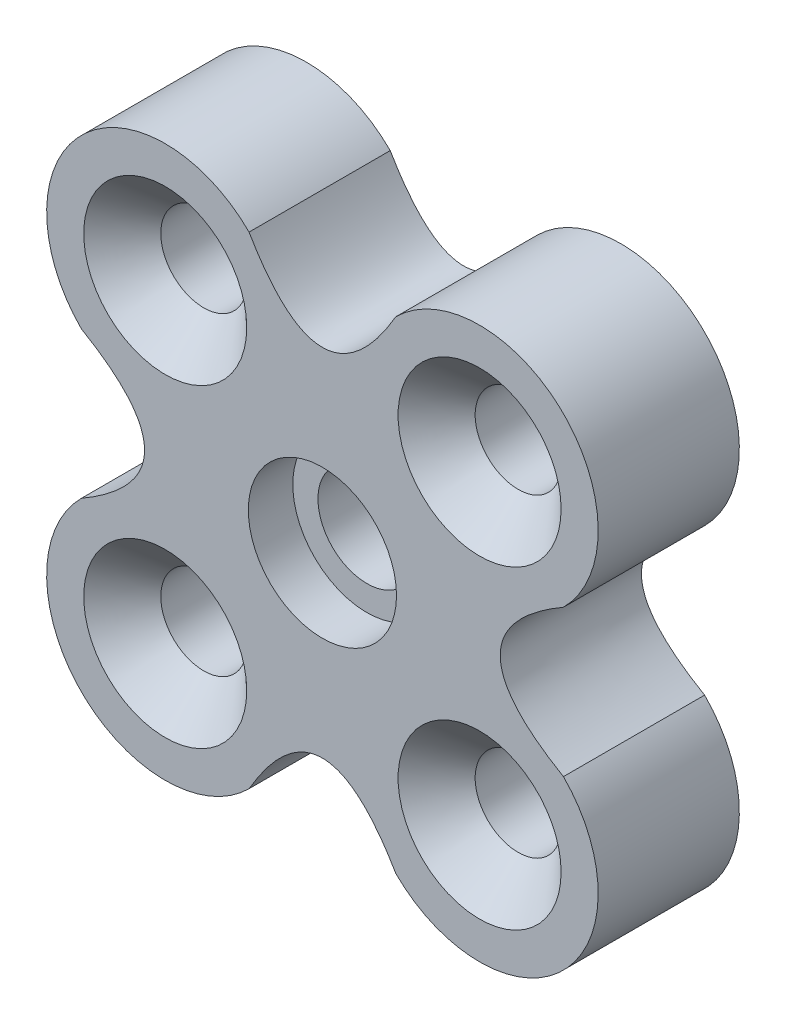
SolidWorks part; units mm, degrees
material "6061-T6 (SS)"
ref_plane "Front Plane" through (0, 0, 0) normal (0, 0, 1) x (1, 0, 0)
ref_plane "Top Plane" through (0, 0, 0) normal (0, 1, 0) x (1, 0, 0)
ref_plane "Right Plane" through (0, 0, 0) normal (1, 0, 0) x (0, 0, -1)
sketch "Sketch1" plane through (0, 0, 0) normal (0, 0, 1) x (1, 0, 0)
  line L0 (0, 0) -> (5.3033, 5.3033) construction
  line L1 (0, 0) -> (-5.3033, 5.3033) construction
  line L2 (0, 0) -> (5.3033, -5.3033) construction
  line L3 (0, 0) -> (-5.3033, -5.3033) construction
  line L4 (0, 0) -> (0, 6) construction
  line L5 (0, 0) -> (6, 0) construction
  line L6 (0, 0) -> (0, -6) construction
  line L7 (0, 0) -> (-6, 0) construction
  arc A4 (-8.1317, 2.4749) -> (-2.4749, 8.1317) centre (-5.3033, 5.3033) cw
  arc A5 (2.4749, 8.1317) -> (8.1317, 2.4749) centre (5.3033, 5.3033) cw
  arc A6 (-8.1317, -2.4749) -> (-2.4749, -8.1317) centre (-5.3033, -5.3033) ccw
  arc A7 (8.1317, -2.4749) -> (2.4749, -8.1317) centre (5.3033, -5.3033) cw
  spline S0 degree 2 poles (-2.4749, 8.1317) (0, 3.8683) (2.4749, 8.1317) knots 0 0 0 1 1 1
  spline S1 degree 2 poles (-8.1317, -2.4749) (-3.8683, 0) (-8.1317, 2.4749) knots 0 0 0 1 1 1
  spline S2 degree 2 poles (8.1317, 2.4749) (3.8683, 0) (8.1317, -2.4749) knots 0 0 0 1 1 1
  spline S3 degree 2 poles (2.4749, -8.1317) (0, -3.8683) (-2.4749, -8.1317) knots 0 0 0 1 1 1
  point P3 (-9.3033, 5.3033)
  point P7 (9.3033, 5.3033)
  point P8 (-5.3033, 9.3033)
  point P9 (-5.3033, -9.3033)
  point P16 (-8.1283, 8.1283)
  point P18 (-2.4749, 8.1317)
  point P19 (8.1456, 8.1456)
  point P20 (-8.1317, 2.4749)
  point P21 (2.4749, 8.1317)
  point P22 (8.1317, 2.4749)
  point P31 (-8.1317, -2.4749)
  point P32 (-8.1317, -8.1317)
  point P33 (-2.4749, -8.1317)
  point P38 (8.1317, -2.4749)
  point P39 (8.1317, -8.1317)
  point P40 (2.4749, -8.1317)
  point P43 (0, 0)
  dimension "D1" = 7.5
  dimension "D2" = 18.6066
  dimension "D3" = 18.6066
extrude "Boss-Extrude1" add sketch "Sketch1" along normal blind 4.763
hole_wizard "CSK for M2.5 Flat Head Machine Screw1" positions "Sketch3" profile "Sketch2" countersink size "M2.5" standard "ANSI Metric" end condition through all
sketch "Sketch3" plane through (0, 0, 4.763) normal (0, 0, 1) x (1, 0, 0)
  line L0 (0, 0) -> (-5.3033, 5.3033) construction
  line L2 (0, 0) -> (5.3033, 5.3033) construction
  line L4 (0, 0) -> (5.3033, -5.3033) construction
  line L6 (0, 0) -> (-5.3033, -5.3033) construction
  point P0 (-5.3033, 5.3033)
  point P2 (5.3033, 5.3033)
  point P4 (5.3033, -5.3033)
  point P6 (-5.3033, -5.3033)
  dimension "D1" = 7.5
  dimension "D2" = 15
  dimension "D3" = 7.5
  dimension "D6" = 15
sketch "Sketch2" plane through (-5.3033, 5.3033, 4.763) normal (1, 0, 0) x (0, -1, 0)
  line L0 (0, 0) -> (0, 4.763)
  line L1 (0, 4.763) -> (1.45, 4.763)
  line L2 (1.45, 4.763) -> (1.45, 1.3)
  line L3 (1.45, 1.3) -> (2.75, 0)
  line L5 (2.75, 0) -> (0, 0)
  line L6 (-1.45, 1.3) -> (-2.75, 0) construction
  line L11 (0, -6.35) -> (0, 107.95) construction
  dimension "Thru Hole Dia." = 2.9
  dimension "Thru Hole Depth" = 4.763
  dimension "Near C'Sink Dia." = 5.5
  dimension "Near C'Sink Angle" = 90
hole_wizard "Tap Drill for M4x0.7 Tap1" positions "Sketch7" profile "Sketch6" hole size "M4x0.7" standard "ANSI Metric" end condition through all
sketch "Sketch7" plane through (0, 0, 4.763) normal (0, 0, 1) x (1, 0, 0)
  point P0 (0, 0)
sketch "Sketch6" plane through (0, 0, 4.763) normal (1, 0, 0) x (0, -1, 0)
  line L0 (0, 0) -> (0, 4.763)
  line L1 (0, 4.763) -> (1.65, 4.763)
  line L2 (1.65, 4.763) -> (1.65, 0)
  line L5 (1.65, 0) -> (0, 0)
  line L11 (0, -6.35) -> (0, 107.95) construction
  dimension "Thru Hole Dia." = 3.3
  dimension "Thru Hole Depth" = 4.763
sketch "Sketch8" plane through (0, 0, 4.763) normal (0, 0, 1) x (1, 0, 0)
  circle A0 centre (0, 0) radius 2.5
extrude "Cut-Extrude1" cut sketch "Sketch8" against normal blind 1.5
